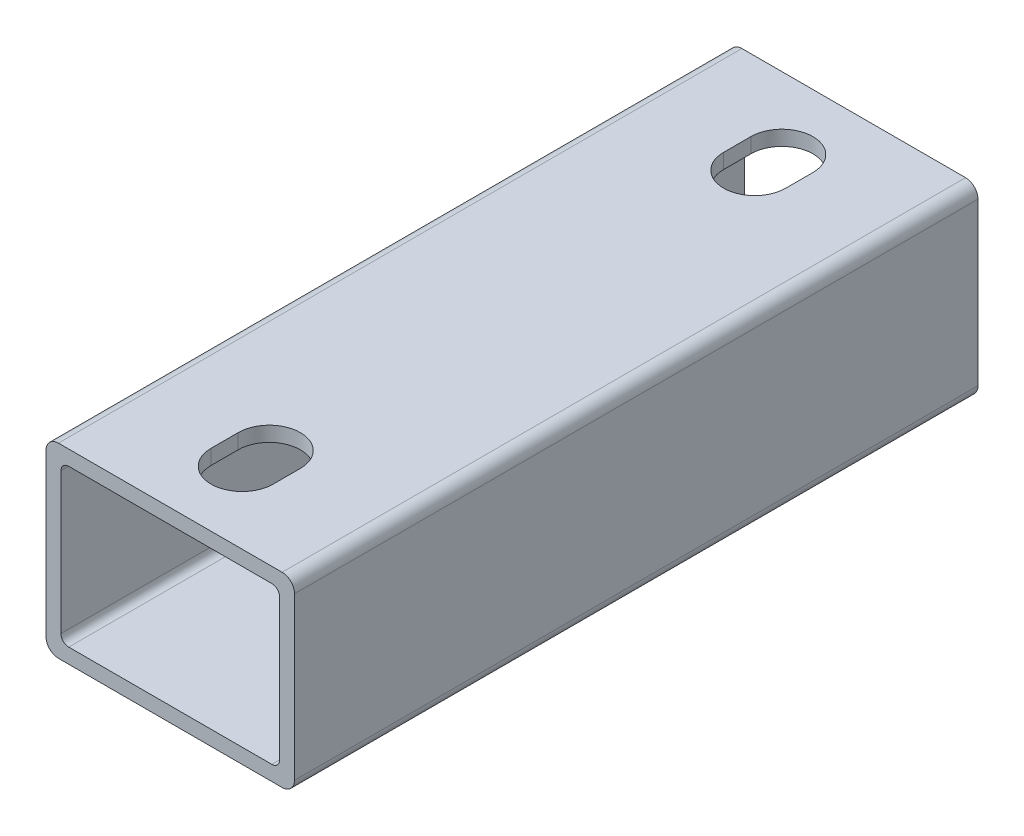
SolidWorks part; units mm, degrees
material "Plain Carbon Steel"
ref_plane "Front" through (0, 0, 0) normal (0, 0, 1) x (1, 0, 0)
ref_plane "Top" through (0, 0, 0) normal (0, 1, 0) x (1, 0, 0)
ref_plane "Right" through (0, 0, 0) normal (1, 0, 0) x (0, 0, -1)
sketch "Sketch1" plane through (0, 0, 0) normal (0, 0, 1) x (1, 0, 0)
  line L0 (-22.352, 0) -> (-25.4, 0) construction
  line L1 (22.86, -19.05) -> (-22.86, -19.05)
  line L2 (25.4, -16.51) -> (25.4, 16.51)
  line L3 (22.86, 19.05) -> (-22.86, 19.05)
  line L4 (-25.4, -16.51) -> (-25.4, 16.51)
  line L5 (25.4, -19.05) -> (-25.4, 19.05) construction
  line L6 (25.4, 19.05) -> (-25.4, -19.05) construction
  line L7 (20.7518, 16.002) -> (-20.7518, 16.002)
  line L8 (22.352, 14.4018) -> (22.352, -14.4018)
  line L9 (20.7518, -16.002) -> (-20.7518, -16.002)
  line L10 (-22.352, 14.4018) -> (-22.352, -14.4018)
  line L11 (22.352, 16.002) -> (-22.352, -16.002) construction
  line L12 (22.352, -16.002) -> (-22.352, 16.002) construction
  line L13 (0, -16.002) -> (0, -19.05) construction
  line L14 (22.352, -14.4018) -> (22.352, -19.05) construction
  line L16 (22.352, -19.05) -> (25.4, -19.05) construction
  arc A0 (-20.7518, -16.002) -> (-22.352, -14.4018) centre (-20.7518, -14.4018) cw
  arc A1 (22.352, -14.4018) -> (20.7518, -16.002) centre (20.7518, -14.4018) cw
  arc A2 (20.7518, 16.002) -> (22.352, 14.4018) centre (20.7518, 14.4018) cw
  arc A3 (-20.7518, 16.002) -> (-22.352, 14.4018) centre (-20.7518, 14.4018) ccw
  arc A4 (22.86, -19.05) -> (25.4, -16.51) centre (22.86, -16.51) ccw
  arc A5 (25.4, 16.51) -> (22.86, 19.05) centre (22.86, 16.51) ccw
  arc A6 (-22.86, 19.05) -> (-25.4, 16.51) centre (-22.86, 16.51) ccw
  arc A7 (-22.86, -19.05) -> (-25.4, -16.51) centre (-22.86, -16.51) cw
  point P0 (0, 0)
  point P6 (0, 0)
  dimension "D2" = 1.6002
  dimension "D3" = 2.54
sketch "Sketch2" plane through (0, 0, 0) normal (1, 0, 0) x (0, 0, -1)
  line L0 (-152.4, 0) -> (152.4, 0) construction
  dimension "Length" = 304.8
ref_plane "Plane1" through (25.4, 0, 0) normal (1, 0, 0) x (0, 0, -1)
sketch "Sketch5" plane through (25.4, 0, 0) normal (1, 0, 0) x (0, 0, -1)
  line L0 (-152.4, 19.05) -> (-152.4, -19.05) construction
  line L1 (152.4, 19.05) -> (152.4, -19.05) construction
sketch "Sketch4" plane through (0, 0, 0) normal (0, 0, 1) x (1, 0, 0)
  line L0 (25.4, -16.51) -> (25.4, 16.51) construction
  line L1 (22.86, 19.05) -> (-22.86, 19.05) construction
  line L2 (-25.4, -16.51) -> (-25.4, 16.51) construction
  line L3 (22.86, -19.05) -> (-22.86, -19.05) construction
  line L4 (22.352, 14.4018) -> (22.352, -14.4018) construction
  line L5 (20.7518, -16.002) -> (-20.7518, -16.002) construction
  line L6 (-22.352, 14.4018) -> (-22.352, -14.4018) construction
  line L7 (20.7518, 16.002) -> (-20.7518, 16.002) construction
  line L8 (25.4, -16.51) -> (25.4, 16.51)
  line L9 (22.86, 19.05) -> (-22.86, 19.05)
  line L10 (-25.4, -16.51) -> (-25.4, 16.51)
  line L11 (22.86, -19.05) -> (-22.86, -19.05)
  line L12 (22.352, 14.4018) -> (22.352, -14.4018)
  line L13 (20.7518, -16.002) -> (-20.7518, -16.002)
  line L14 (-22.352, 14.4018) -> (-22.352, -14.4018)
  line L15 (20.7518, 16.002) -> (-20.7518, 16.002)
  arc A0 (25.4, 16.51) -> (22.86, 19.05) centre (22.86, 16.51) ccw construction
  arc A1 (-22.86, 19.05) -> (-25.4, 16.51) centre (-22.86, 16.51) ccw construction
  arc A2 (-25.4, -16.51) -> (-22.86, -19.05) centre (-22.86, -16.51) ccw construction
  arc A3 (22.86, -19.05) -> (25.4, -16.51) centre (22.86, -16.51) ccw construction
  arc A4 (20.7518, -16.002) -> (22.352, -14.4018) centre (20.7518, -14.4018) ccw construction
  arc A5 (-22.352, -14.4018) -> (-20.7518, -16.002) centre (-20.7518, -14.4018) ccw construction
  arc A6 (-20.7518, 16.002) -> (-22.352, 14.4018) centre (-20.7518, 14.4018) ccw construction
  arc A7 (22.352, 14.4018) -> (20.7518, 16.002) centre (20.7518, 14.4018) ccw construction
  arc A8 (25.4, 16.51) -> (22.86, 19.05) centre (22.86, 16.51) ccw
  arc A9 (-22.86, 19.05) -> (-25.4, 16.51) centre (-22.86, 16.51) ccw
  arc A10 (-25.4, -16.51) -> (-22.86, -19.05) centre (-22.86, -16.51) ccw
  arc A11 (22.86, -19.05) -> (25.4, -16.51) centre (22.86, -16.51) ccw
  arc A12 (20.7518, -16.002) -> (22.352, -14.4018) centre (20.7518, -14.4018) ccw
  arc A13 (-22.352, -14.4018) -> (-20.7518, -16.002) centre (-20.7518, -14.4018) ccw
  arc A14 (-20.7518, 16.002) -> (-22.352, 14.4018) centre (-20.7518, 14.4018) ccw
  arc A15 (22.352, 14.4018) -> (20.7518, 16.002) centre (20.7518, 14.4018) ccw
extrude "Boss-Extrude1" add sketch "Sketch4" along normal blind 139.7
sketch "Sketch6" plane through (0, 19.05, 0) normal (0, 1, 0) x (1, 0, 0)
  line L0 (22.86, -139.7) -> (-22.86, -139.7) construction
  line L8 (0, -139.7) -> (0, 0) construction
  line L9 (22.86, 0) -> (-22.86, 0) construction
sketch "Sketch7" plane through (0, 19.05, 0) normal (0, 1, 0) x (1, 0, 0)
  line L0 (-6.35, -20.2406) -> (-6.35, -14.6844) construction
  line L1 (6.35, -14.6844) -> (6.35, -20.2406) construction
  line L2 (-6.35, -125.0156) -> (-6.35, -119.4594) construction
  line L3 (6.35, -119.4594) -> (6.35, -125.0156) construction
  line L4 (-6.35, -20.2406) -> (-6.35, -14.6844)
  line L5 (6.35, -14.6844) -> (6.35, -20.2406)
  line L6 (-6.35, -125.0156) -> (-6.35, -119.4594)
  line L7 (6.35, -119.4594) -> (6.35, -125.0156)
  arc A0 (6.35, -14.6844) -> (-6.35, -14.6844) centre (0, -14.6844) ccw construction
  arc A1 (-6.35, -20.2406) -> (6.35, -20.2406) centre (0, -20.2406) ccw construction
  arc A2 (-6.35, -125.0156) -> (6.35, -125.0156) centre (0, -125.0156) ccw construction
  arc A3 (6.35, -119.4594) -> (-6.35, -119.4594) centre (0, -119.4594) ccw construction
  arc A4 (6.35, -14.6844) -> (-6.35, -14.6844) centre (0, -14.6844) ccw
  arc A5 (-6.35, -20.2406) -> (6.35, -20.2406) centre (0, -20.2406) ccw
  arc A6 (-6.35, -125.0156) -> (6.35, -125.0156) centre (0, -125.0156) ccw
  arc A7 (6.35, -119.4594) -> (-6.35, -119.4594) centre (0, -119.4594) ccw
extrude "Cut-Extrude1" cut sketch "Sketch7" along direction (0, -1, 0) on the side against the normal up to next (3.048 mm away)
equation "\"D3@Sketch1\"=\"Outside Width@Sketch1\"*.05"
equation "\"D2@Sketch1\"=\"D1@Sketch1\"*.05"
